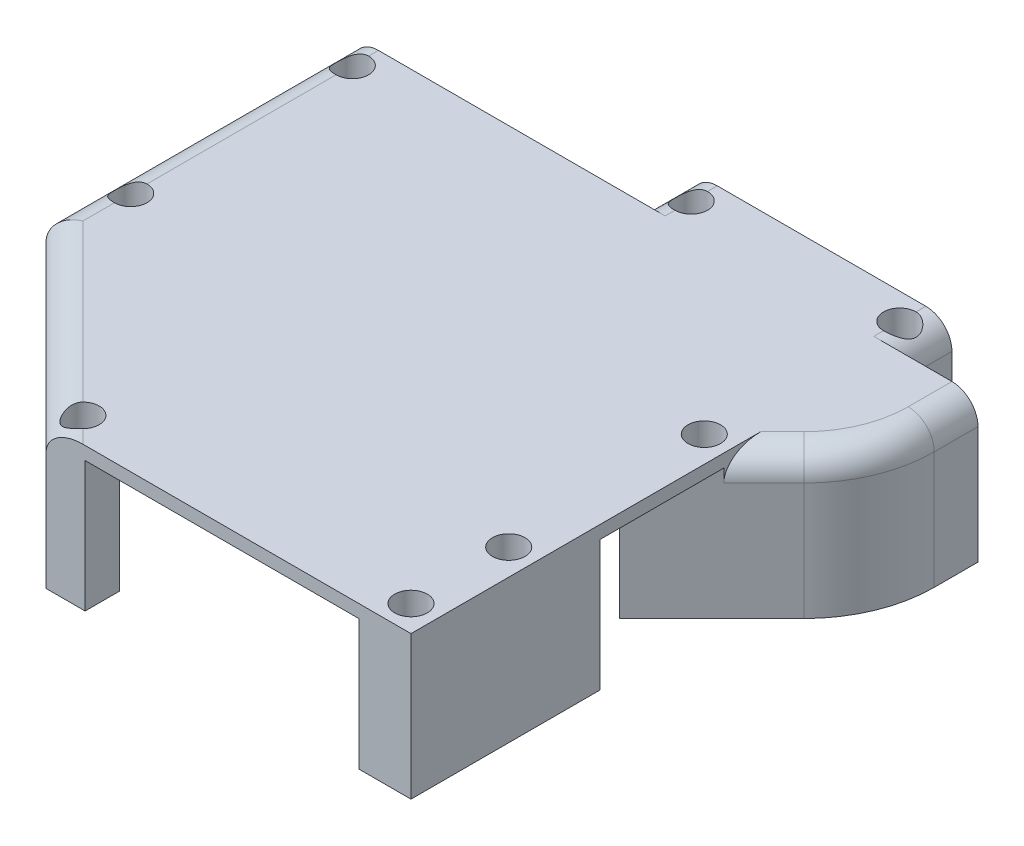
SolidWorks part; units mm, degrees
ref_plane "Front" through (0, 0, 0) normal (0, 0, 1) x (1, 0, 0)
ref_plane "Top" through (0, 0, 0) normal (0, 1, 0) x (1, 0, 0)
ref_plane "Right" through (0, 0, 0) normal (1, 0, 0) x (0, 0, -1)
sketch "Sketch3" plane through (0, 0, 0) normal (0, 1, 0) x (1, 0, 0)
  line L0 (-2.6315, 29.2915) -> (-6.6315, 29.2915)
  line L1 (-6.6315, 29.2915) -> (-6.6315, 5.7915)
  line L2 (-6.6315, 5.7915) -> (7.3685, -8.2085)
  line L3 (12.0254, -7.2085) -> (31.3685, -7.2085)
  line L4 (7.3685, -8.2085) -> (35.3685, -8.2085)
  line L5 (9.3685, 29.2915) -> (15.3685, 29.2915)
  line L6 (19.3685, 28.2915) -> (9.3685, 28.2915)
  line L7 (34.3685, -0.7085) -> (31.3685, -0.7085)
  line L8 (-2.6315, 25.2915) -> (-5.6315, 25.2915)
  line L9 (9.3685, 28.2915) -> (9.3685, 29.2915)
  line L10 (-2.6315, 29.2915) -> (9.3685, 29.2915) construction
  line L11 (3.3685, 29.2915) -> (3.3685, 27.2915) construction
  line L12 (3.3685, 27.2915) -> (-4.6315, 27.2915) construction
  line L13 (3.3685, 27.2915) -> (11.3685, 27.2915) construction
  line L14 (3.3685, 27.2915) -> (3.3685, 17.2915) construction
  line L15 (3.3685, 10.2915) -> (3.3685, 5.7915) construction
  line L16 (-5.6315, 25.2915) -> (-5.6315, 12.2915)
  line L17 (3.3685, 17.2915) -> (11.3685, 17.2915) construction
  line L18 (-5.6315, 12.2915) -> (-2.6315, 12.2915)
  line L19 (19.3685, 33.2915) -> (19.3685, 28.2915)
  line L20 (3.3685, 5.7915) -> (3.3685, -6.2085) construction
  line L21 (3.3685, -6.2085) -> (8.3685, -6.2085) construction
  line L22 (-2.6315, 29.2915) -> (-2.6315, 25.2915)
  line L24 (3.3685, 17.2915) -> (3.3685, 10.2915) construction
  line L25 (3.3685, 10.2915) -> (-4.6315, 10.2915) construction
  line L26 (31.3685, 33.2915) -> (35.3685, 33.2915)
  line L27 (34.3685, -4.2085) -> (31.3685, -4.2085)
  line L29 (31.3685, -4.2085) -> (31.3685, -7.2085)
  line L30 (35.3685, 29.2915) -> (35.3685, 33.2915)
  line L31 (12.0254, -7.2085) -> (-2.6315, 7.4483)
  line L32 (-2.6315, 7.4483) -> (-2.6315, 12.2915)
  line L33 (34.3685, -0.7085) -> (34.3685, -4.2085)
  line L34 (34.3685, 5.3062) -> (31.3685, 2.3062)
  line L35 (35.3685, 29.2915) -> (41.3685, 29.2915)
  line L36 (31.3685, 2.3062) -> (31.3685, -0.7085)
  line L37 (25.3685, 1.2915) -> (33.3685, 1.2915) construction
  line L38 (19.3685, 33.2915) -> (15.3685, 33.2915)
  line L39 (34.3685, 29.2915) -> (34.3685, 28.2915)
  line L40 (15.3685, 29.2915) -> (15.3685, 33.2915)
  line L41 (25.3685, 1.2915) -> (25.3685, -6.2085) construction
  line L42 (41.3685, 29.2915) -> (41.3685, 21.7915)
  line L43 (31.3685, 33.2915) -> (31.3685, 29.2915)
  line L44 (25.3685, 16.2915) -> (33.3685, 16.2915) construction
  line L45 (19.3685, 33.2915) -> (31.3685, 33.2915) construction
  line L46 (25.3685, 33.2915) -> (25.3685, 31.2915) construction
  line L47 (25.3685, 31.2915) -> (17.3685, 31.2915) construction
  line L48 (25.3685, 31.2915) -> (33.3685, 31.2915) construction
  line L49 (35.3685, 15.7915) -> (35.3685, -8.2085)
  line L50 (39.3685, 28.2915) -> (34.3685, 28.2915)
  line L51 (25.3685, 31.2915) -> (25.3685, 16.2915) construction
  line L52 (25.3685, 16.2915) -> (25.3685, 1.2915) construction
  line L53 (35.3685, 15.7915) -> (41.3685, 21.7915)
  line L55 (31.3685, 18.2915) -> (35.0401, 18.2915)
  line L56 (35.0401, 18.2915) -> (39.3685, 22.6199)
  line L57 (31.3685, 29.2915) -> (34.3685, 29.2915)
  line L60 (31.3685, 18.2915) -> (31.3685, 11.7915)
  line L61 (31.3685, 11.7915) -> (34.3685, 14.7915)
  line L62 (25.3685, 16.2915) -> (17.3685, 16.2915) construction
  line L64 (25.3685, -6.2085) -> (33.3685, -6.2085) construction
  line L65 (34.3685, 5.3062) -> (34.3685, 14.7915)
  line L67 (25.3685, 1.2915) -> (17.3685, 1.2915) construction
  line L69 (39.3685, 22.6199) -> (39.3685, 28.2915)
extrude "Boss-Extrude2" add sketch "Sketch3" along normal blind 11
sketch "Sketch5" plane through (0, 0, 0) normal (0, 1, 0) x (1, 0, 0)
  line L0 (-6.6315, 29.2915) -> (15.3685, 29.2915)
  line L1 (-6.6315, 5.7915) -> (7.3685, -8.2085)
  line L2 (7.3685, -8.2085) -> (35.3685, -8.2085)
  line L3 (35.3685, 33.2915) -> (35.3685, 29.2915)
  line L4 (-6.6315, 5.7915) -> (-6.6315, 29.2915)
  line L5 (15.3685, 29.2915) -> (15.3685, 33.2915)
  line L6 (15.3685, 33.2915) -> (35.3685, 33.2915)
  line L7 (35.3685, 29.2915) -> (41.3685, 29.2915)
  line L8 (41.3685, 29.2915) -> (41.3685, 21.7915)
  line L9 (41.3685, 21.7915) -> (35.3685, 15.7915)
  line L10 (35.3685, 15.7915) -> (35.3685, -8.2085)
extrude "Boss-Extrude3" add sketch "Sketch5" against normal blind 1 from offset 11
fillet "Fillet2" radius 10 1 edges at (41.3685, 5.5, -21.7915)
fillet "Fillet1" radius 2 6 edges at (36.9041, 11, -17.327) (41.3685, 11, -27.6125) (15.3685, 11, -31.2915) (40.6073, 11, -22.1068) (-6.6315, 11, -17.5415) (0.3685, 11, 1.2085)
sketch "Sketch14" plane through (0, 0, 0) normal (0, 1, 0) x (1, 0, 0)
  line L0 (31.3685, 11.7915) -> (35.3685, 15.7915)
  line L1 (35.3685, 15.7915) -> (35.3685, 17.7915)
  line L2 (35.3685, 17.7915) -> (31.3685, 13.7915)
  line L4 (31.3685, 13.7915) -> (31.3685, 11.7915)
extrude "Boss-Extrude4" add sketch "Sketch14" along normal blind 11
sketch "Sketch7" plane through (0, 0, 0) normal (0, 1, 0) x (1, 0, 0)
  line L0 (3.3685, 29.2915) -> (3.3685, 27.2915) construction
  line L2 (3.3685, 27.2915) -> (-4.6315, 27.2915) construction
  line L3 (3.3685, 27.2915) -> (11.3685, 27.2915) construction
  line L4 (3.3685, 27.2915) -> (3.3685, 17.2915) construction
  line L5 (25.3685, 1.2915) -> (33.3685, 1.2915) construction
  line L6 (25.3685, 1.2915) -> (25.3685, -6.2085) construction
  line L7 (25.3685, 16.2915) -> (33.3685, 16.2915) construction
  line L9 (25.3685, 33.2915) -> (25.3685, 31.2915) construction
  line L10 (25.3685, 31.2915) -> (17.3685, 31.2915) construction
  line L12 (3.3685, 17.2915) -> (3.3685, 10.2915) construction
  line L13 (3.3685, 10.2915) -> (-4.6315, 10.2915) construction
  line L14 (25.3685, 31.2915) -> (33.3685, 31.2915) construction
  line L15 (25.3685, 31.2915) -> (25.3685, 16.2915) construction
  line L16 (25.3685, 16.2915) -> (25.3685, 1.2915) construction
  line L17 (8.2828, -6.2943) -> (6.8685, -7.7085) construction
  line L18 (25.3685, -6.2085) -> (33.3685, -6.2085) construction
  line L19 (7.3685, -8.2085) -> (-6.6315, 5.7915) construction
  circle A0 centre (-4.6315, 27.2915) radius 0.8
  circle A2 centre (17.3685, 31.2915) radius 0.8
  circle A3 centre (33.3685, 31.2915) radius 0.8
  circle A4 centre (-4.6315, 10.2915) radius 0.8
  circle A5 centre (33.3685, 16.2915) radius 0.8
  circle A6 centre (8.2828, -6.2943) radius 0.8
  circle A8 centre (33.3685, 1.2915) radius 0.8
  circle A9 centre (33.3685, -6.2085) radius 0.8
sketch "Sketch10" plane through (0, 0, 0) normal (0, 1, 0) x (1, 0, 0)
  line L0 (34.3685, 5.3062) -> (35.3685, 6.3062)
  line L1 (34.3685, 14.7915) -> (35.3685, 15.7915)
  line L2 (10.3685, -5.5517) -> (10.3685, -8.2085)
  line L4 (17.5254, -3.5162) -> (6.9188, 7.0904)
  line L5 (10.3685, -8.2085) -> (31.3685, -8.2085)
  line L6 (10.3685, -5.5517) -> (2.3226, 2.4943)
  line L7 (6.9188, 7.0904) -> (2.3226, 2.4943)
  line L8 (31.3685, -8.2085) -> (31.3685, -3.5162)
  line L9 (31.3685, -3.5162) -> (17.5254, -3.5162)
  line L12 (35.3685, 15.7915) -> (35.3685, 6.3062)
  line L13 (34.3685, 5.3062) -> (34.3685, 14.7915)
  line L14 (35.3685, 33.2915) -> (35.3685, 15.7915) construction
extrude "Tube Holes" cut sketch "Sketch10" along normal blind 10
sketch "Sketch9" plane through (-0.42, 0, 0.42) normal (-0.7071, 0, 0.7071) x (0.7071, 0, 0.7071)
  line L0 (-8.2843, 0) -> (-2.7843, 0) construction
  line L1 (-2.7843, 0) -> (6.7157, 0) construction
  line L2 (-2.7843, 0) -> (-2.7843, 5.5) construction
  line L3 (-2.7843, 0) -> (-2.7843, -5.5) construction
  line L4 (-8.2843, -1.5) -> (-6.7843, -1.5) construction
  line L5 (-6.7843, -1.5) -> (-6.7843, -4.5) construction
  line L6 (-8.2843, -1.5) -> (-6.7843, -4.5)
  line L7 (-6.7843, -4.5) -> (-6.7843, -5.5)
  line L8 (-6.7843, -5.5) -> (-2.7843, -5.5)
  line L9 (-2.7843, -5.5) -> (1.4657, -5.5)
  line L10 (1.4657, -5.5) -> (1.4657, -4.5)
  line L11 (1.4657, -4.5) -> (6.7157, -4.5)
  line L12 (6.7157, -4.5) -> (6.7157, 0)
  line L13 (-8.2843, 1.5) -> (-6.7843, 1.5) construction
  line L14 (-6.7843, 1.5) -> (-6.7843, 4.5) construction
  line L15 (-8.2843, 1.5) -> (-6.7843, 4.5)
  line L16 (-6.7843, 4.5) -> (-6.7843, 5.5)
  line L17 (-6.7843, 5.5) -> (-2.7843, 5.5)
  line L18 (-2.7843, 5.5) -> (1.4657, 5.5)
  line L19 (1.4657, 5.5) -> (1.4657, 4.5)
  line L20 (1.4657, 4.5) -> (6.7157, 4.5)
  line L21 (6.7157, 4.5) -> (6.7157, 0)
  line L22 (-2.7843, 5) -> (-2.7843, 0) construction
  line L23 (-8.2843, 1.5) -> (-8.2843, 0)
  line L24 (-8.2843, 0) -> (-8.2843, -1.5)
  line L26 (-2.7843, -5) -> (-2.7843, 0) construction
extrude "Pot Insert" cut sketch "Sketch9" against normal blind 2.5
sketch "Sketch13" plane through (-0.42, 0, 0.42) normal (-0.7071, 0, 0.7071) x (0.7071, 0, 0.7071)
  line L0 (-8.7843, 0) -> (-2.7843, 0) construction
  line L1 (-2.7843, 0) -> (6.7157, 0) construction
  line L2 (6.7157, 0) -> (6.7157, 2.5)
  line L4 (6.7157, 2.5) -> (4.7157, 2.5)
  line L5 (4.7157, 2.5) -> (4.7157, -2.5)
  line L6 (4.7157, -2.5) -> (6.7157, -2.5)
  line L7 (6.7157, -2.5) -> (6.7157, 0)
  circle A0 centre (-2.7843, 0) radius 2.75
extrude "Pot Hole" cut sketch "Sketch13" against normal blind 1.5 from offset 2.5
extrude "Screw Holes" cut sketch "Sketch7" along normal through all
sketch "Sketch12" plane through (0, 0, 0) normal (0, 1, 0) x (1, 0, 0)
  circle A0 centre (-4.6315, 27.2915) radius 1.25
  circle A2 centre (17.3685, 31.2915) radius 1.25
  circle A3 centre (33.3685, 31.2915) radius 1.25
  circle A4 centre (-4.6315, 10.2915) radius 1.25
  circle A5 centre (33.3685, 16.2915) radius 1.25
  circle A6 centre (8.2828, -6.2943) radius 1.25
  circle A7 centre (33.3685, 1.2915) radius 1.25
  circle A8 centre (33.3685, -6.2085) radius 1.25
extrude "Screw Heads" cut sketch "Sketch12" against normal blind 3 from offset 11
